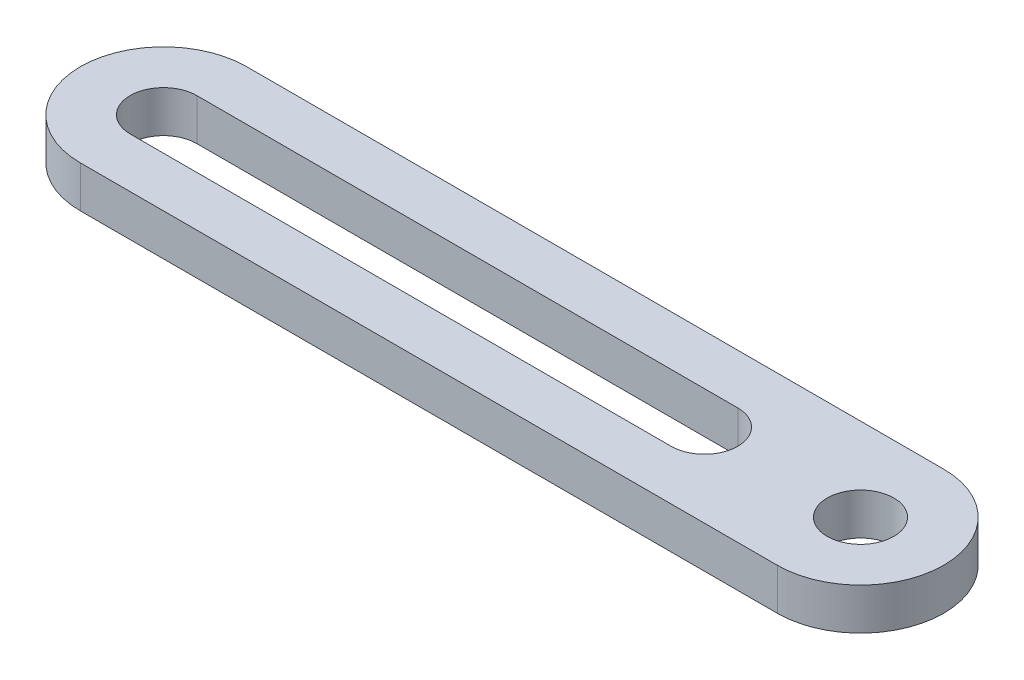
SolidWorks part; units mm, degrees
material "Thornel Mat VMA"
ref_plane "前视基准面" through (0, 0, 0) normal (0, 0, 1) x (1, 0, 0)
ref_plane "上视基准面" through (0, 0, 0) normal (0, 1, 0) x (1, 0, 0)
ref_plane "右视基准面" through (0, 0, 0) normal (1, 0, 0) x (0, 0, -1)
sketch "草图1" plane through (0, 0, 0) normal (0, 1, 0) x (1, 0, 0)
  line L0 (0, 0) -> (-33.5, 0) construction
  line L1 (0, -4) -> (-33.5, -4)
  line L2 (0, 4) -> (-33.5, 4)
  line L3 (-33.5, 0) -> (-7.5, 0) construction
  line L4 (-33.5, 1.6) -> (-7.5, 1.6)
  line L5 (-33.5, -1.6) -> (-7.5, -1.6)
  arc A0 (0, -4) -> (0, 4) centre (0, 0) ccw
  arc A1 (-33.5, 4) -> (-33.5, -4) centre (-33.5, 0) ccw
  arc A2 (-33.5, 1.6) -> (-33.5, -1.6) centre (-33.5, 0) ccw
  arc A3 (-7.5, -1.6) -> (-7.5, 1.6) centre (-7.5, 0) ccw
  circle A4 centre (0, 0) radius 1.6
  point P3 (-16.75, 0)
  point P8 (-20.5, 0)
  dimension "D1" = 3.2
  dimension "D3" = 4
  dimension "D4" = 7.5
  dimension "D2" = 3.2
  dimension "D5" = 33.5
extrude "凸台-拉伸1" add sketch "草图1" along normal blind 2
ref_plane "基准面1" through (-29.5, 0, 0) normal (1, 0, 0) x (0, 0, -1)
